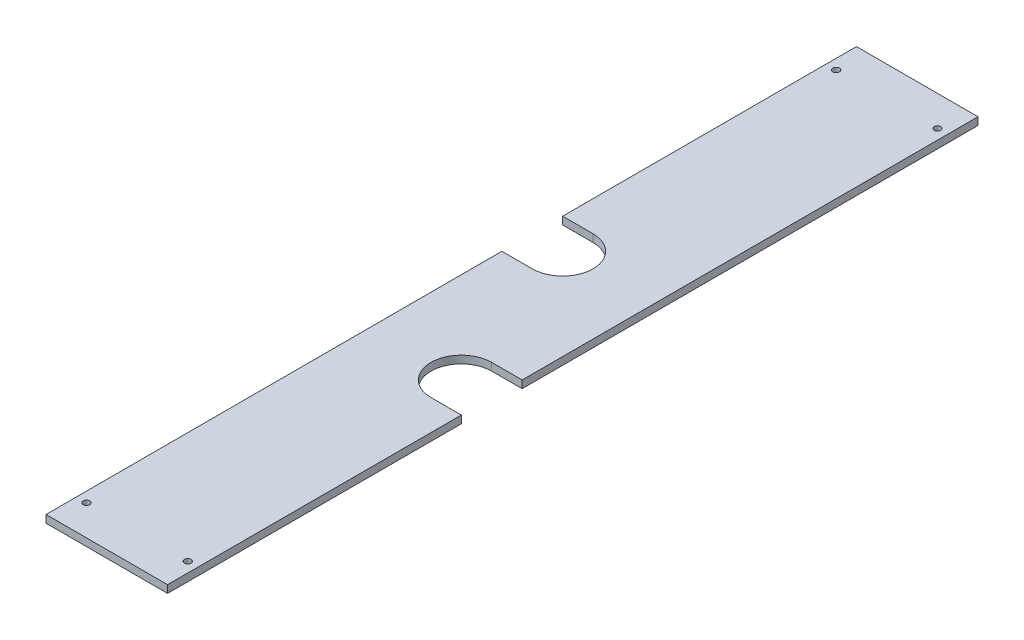
SolidWorks part; units mm, degrees
ref_plane "Front Plane" through (0, 0, 0) normal (0, 0, 1) x (1, 0, 0)
ref_plane "Top Plane" through (0, 0, 0) normal (0, 1, 0) x (1, 0, 0)
ref_plane "Right Plane" through (0, 0, 0) normal (1, 0, 0) x (0, 0, -1)
sketch "Sketch1" plane through (0, 0, 0) normal (0, 0, 1) x (1, 0, 0)
  line L0 (-38.0447, -22.987) -> (38.0447, -22.987) construction
  line L1 (-38.1, -16.637) -> (38.1, -16.637) construction
  line L2 (-38.1, -16.637) -> (-38.1, -13.462) construction
  line L3 (-38.1, -13.462) -> (38.1, -13.462) construction
  line L4 (38.1, -16.637) -> (38.1, -13.462) construction
  line L5 (-38.1, 22.8953) -> (38.1, 22.8953)
  line L6 (-38.1, 22.8953) -> (-38.1, 18.1328)
  line L7 (-38.1, 18.1328) -> (38.1, 18.1328)
  line L8 (38.1, 22.8953) -> (38.1, 18.1328)
  line L9 (-39.7905, -19.812) -> (39.7905, -19.812) construction
  circle A0 centre (0, 0) radius 44.45 construction
  circle A1 centre (0, 0) radius 47.625 construction
  point P12 (0, -47.625)
  dimension "D1" = 88.9
  dimension "D5" = 95.25
  dimension "D2" = 3.175
  dimension "D3" = 4.7625
  dimension "D4" = 76.2
  dimension "D6" = 24.638
  dimension "D7" = 3.175
  dimension "D8" = 3.175
extrude "Boss-Extrude1" add sketch "Sketch1" along normal blind 508 contours L3 L4 L1 L2 | L7 L8 L5 L6
sketch "Sketch2" plane through (0, 22.8953, 0) normal (0, 1, 0) x (1, 0, 0)
  line L0 (-38.1, -508) -> (38.1, -508) construction
  line L1 (-38.1, -508) -> (-38.1, 0) construction
  line L2 (-19.05, -184.15) -> (-38.1, -184.15)
  line L3 (-38.1, -184.15) -> (-38.1, -222.25)
  line L4 (-38.1, -222.25) -> (-19.05, -222.25)
  line L5 (38.1, -508) -> (38.1, 0) construction
  line L6 (19.05, -323.85) -> (38.1, -323.85)
  line L7 (38.1, -323.85) -> (38.1, -285.75)
  line L8 (38.1, -285.75) -> (19.05, -285.75)
  line L9 (-38.1, 0) -> (38.1, 0) construction
  arc A0 (-19.05, -222.25) -> (-19.05, -184.15) centre (-19.05, -203.2) ccw
  arc A1 (19.05, -285.75) -> (19.05, -323.85) centre (19.05, -304.8) ccw
  dimension "D1" = 304.8
  dimension "D2" = 38.1
  dimension "D4" = 38.1
  dimension "D3" = 19.05
  dimension "D5" = 19.05
  dimension "D6" = 304.8
extrude "Cut-Extrude1" cut sketch "Sketch2" against normal through all
ref_plane "Plane1" through (0, 0, 254) normal (0, 0, 1) x (1, 0, 0)
sketch "Sketch3" plane through (0, 22.8953, 0) normal (0, 1, 0) x (1, 0, 0)
  line L0 (38.1, -285.75) -> (38.1, 0) construction
  line L1 (-38.1, 0) -> (38.1, 0) construction
  line L2 (-38.1, -508) -> (38.1, -508) construction
  line L3 (-38.1, -508) -> (-38.1, -222.25) construction
  circle A0 centre (-31.75, -488.95) radius 2.0828
  circle A1 centre (31.75, -19.05) radius 2.0828
  dimension "D1" = 4.1656
  dimension "D6" = 4.1656
  dimension "D2" = 6.35
  dimension "D3" = 19.05
  dimension "D4" = 19.05
  dimension "D5" = 6.35
extrude "Cut-Extrude2" cut sketch "Sketch3" against normal through all
mirror "Mirror1" about plane through (0, 0, 254) normal (0, 0, 1) of "Cut-Extrude2"
